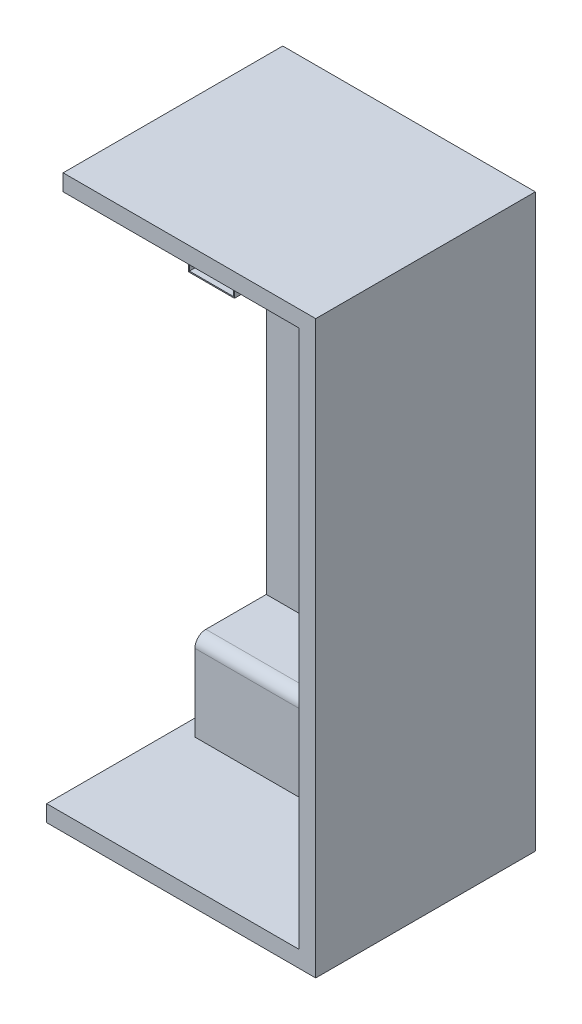
SolidWorks part; units mm, degrees
ref_plane "Front Plane" through (0, 0, 0) normal (0, 0, 1) x (1, 0, 0)
ref_plane "Top Plane" through (0, 0, 0) normal (0, 1, 0) x (1, 0, 0)
ref_plane "Right Plane" through (0, 0, 0) normal (1, 0, 0) x (0, 0, -1)
sketch "Sketch1" plane through (0, 0, 0) normal (0, 0, 1) x (1, 0, 0)
  line L0 (-245, -520) -> (-245, 520)
  line L1 (-215, -490) -> (215, -490)
  line L2 (-215, -490) -> (-215, 490)
  line L3 (-215, 490) -> (215, 490)
  line L4 (215, -490) -> (215, 490)
  line L5 (-215, -490) -> (215, 490) construction
  line L6 (-215, 490) -> (215, -490) construction
  line L7 (-245, 520) -> (245, 520)
  line L8 (245, -520) -> (245, 520)
  line L9 (-245, -520) -> (245, -520)
  point P0 (0, 0)
  dimension "D1" = 980
  dimension "D2" = 430
  dimension "D3" = 30
extrude "Boss-Extrude1" add sketch "Sketch1" along normal blind 370
sketch "Sketch2" plane through (0, 0, 0) normal (0, 0, -1) x (-1, 0, 0)
  line L1 (-245, 520) -> (245, 520)
  line L2 (-245, 520) -> (-245, -520)
  line L3 (-245, -520) -> (245, -520)
  line L4 (245, 520) -> (245, -520)
extrude "Boss-Extrude2" add sketch "Sketch2" along normal blind 30
sketch "Sketch3" plane through (0, 0, 0) normal (0, 0, 1) x (1, 0, 0)
  line L0 (215, -490) -> (215, 490) construction
  line L1 (-215, -490) -> (215, -490)
  line L2 (-215, -490) -> (-215, -330)
  line L3 (-215, -330) -> (215, -330)
  line L4 (215, -490) -> (215, -330)
  dimension "D1" = 160
extrude "Boss-Extrude3" add sketch "Sketch3" along normal blind 130
fillet "Fillet1" radius 20 1 edges at (0, -330, 130)
sketch "Sketch5" plane through (0, 0, 370) normal (0, 0, 1) x (1, 0, 0)
  line L1 (-245, 520) -> (-215, 520)
  line L2 (-245, 520) -> (-245, -490)
  line L3 (-245, -490) -> (-215, -490)
  line L4 (-215, 520) -> (-215, -490)
extrude "Cut-Extrude2" cut sketch "Sketch5" against normal up to surface (400 mm away) up to face at (0, 0, -30)
sketch "Sketch7" plane through (215, 0, 0) normal (-1, 0, 0) x (0, 0, 1)
  line L0 (370, 490) -> (0, 490) construction
  line L1 (0, 490) -> (0, -330) construction
  line L3 (-30, -490) -> (370, -490) construction
  circle A0 centre (160, 280) radius 3
  circle A1 centre (160, 160) radius 3
  circle A2 centre (160, 40) radius 3
  circle A3 centre (160, -80) radius 3
  circle A4 centre (160, -200) radius 3
  dimension "D1" = 210
  dimension "D4" = 6
  dimension "D2" = 5
  dimension "D3" = 160
extrude "Boss-Extrude4" add sketch "Sketch7" along normal blind 50
sketch "Sketch8" plane through (0, 0, 0) normal (0, 0, 1) x (1, 0, 0)
  line L0 (215, 490) -> (-215, 490) construction
  line L1 (-55, 490) -> (25, 490)
  line L2 (-55, 490) -> (-55, 410)
  line L3 (-55, 410) -> (25, 410)
  line L4 (25, 490) -> (25, 410)
  line L5 (215, -330) -> (215, 490) construction
  line L6 (-57, 408) -> (27, 408)
  line L7 (27, 492) -> (27, 408)
  line L8 (-57, 492) -> (27, 492)
  line L9 (-57, 492) -> (-57, 408)
  dimension "D1" = 80
  dimension "D2" = 80
  dimension "D3" = 190
  dimension "D4" = 2
extrude "Boss-Extrude5" add sketch "Sketch8" along normal blind 300
sketch "Sketch9" plane through (0, 0, 0) normal (0, 0, 1) x (1, 0, 0)
  line L1 (-57, 408) -> (27, 408)
  line L2 (-57, 408) -> (-57, 490)
  line L3 (-57, 490) -> (27, 490)
  line L4 (27, 408) -> (27, 490)
extrude "Cut-Extrude3" cut sketch "Sketch9" along normal blind 100
